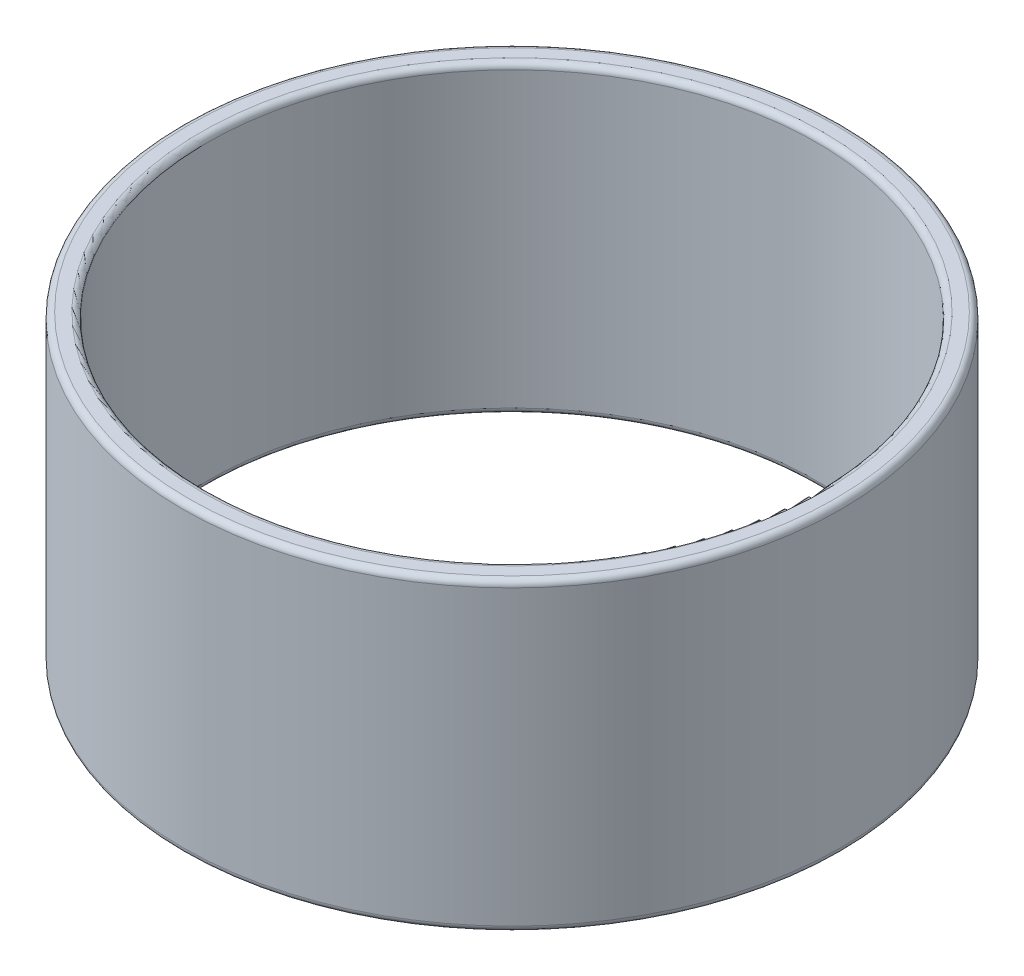
SolidWorks part; units mm, degrees
ref_plane "Спереди" through (0, 0, 0) normal (0, 0, 1) x (1, 0, 0)
ref_plane "Сверху" through (0, 0, 0) normal (0, 1, 0) x (1, 0, 0)
ref_plane "Справа" through (0, 0, 0) normal (1, 0, 0) x (0, 0, -1)
sketch "Эскиз1" plane through (0, 0, 0) normal (0, 1, 0) x (1, 0, 0)
  circle A0 centre (0, 0) radius 25
  circle A1 centre (0, 0) radius 27
  dimension "D2" = 50
  dimension "D1" = 2
extrude "Бобышка-Вытянуть1" add sketch "Эскиз1" along normal blind 25
fillet "Скругление1" radius 0.5 4 edges at (0, 0, 25) (0, 0, 27) (0, 25, 25) (0, 25, 27)
